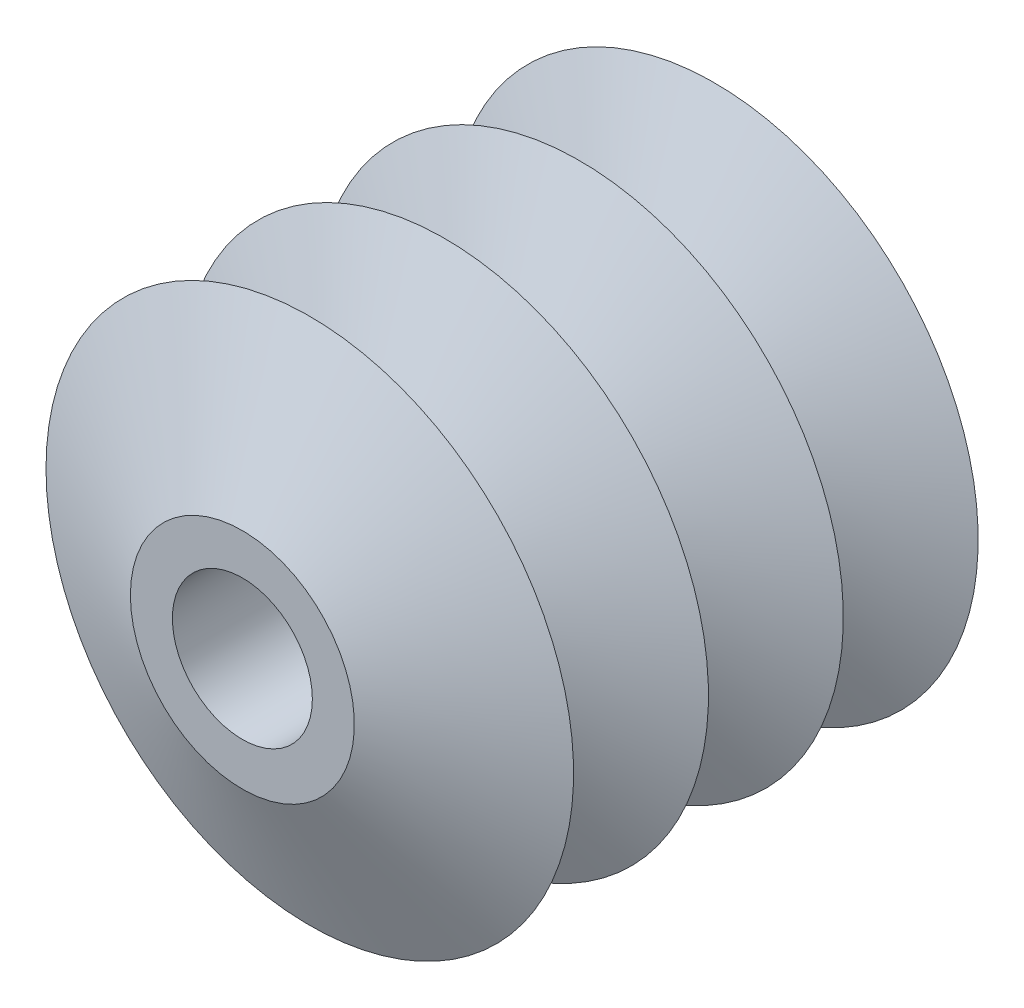
SolidWorks part; units mm, degrees
ref_plane "Front Plane" through (0, 0, 0) normal (0, 0, 1) x (1, 0, 0)
ref_plane "Top Plane" through (0, 0, 0) normal (0, 1, 0) x (1, 0, 0)
ref_plane "Right Plane" through (0, 0, 0) normal (1, 0, 0) x (0, 0, -1)
sketch "Croquis1" plane through (0, 0, 0) normal (0, 1, 0) x (1, 0, 0)
  line L0 (0, 33.7213) -> (0, -33.7213)
  line L1 (0, 33.7213) -> (14, 33.7213)
  line L2 (0, -33.7213) -> (14, -33.7213)
  line L9 (14, -33.7213) -> (32.9802, -25.291)
  line L10 (32.9802, -25.291) -> (14, -16.8606)
  line L11 (14, -16.8606) -> (32.9802, -8.4303)
  line L12 (32.9802, -8.4303) -> (14, 0)
  line L13 (14, 0) -> (32.9802, 8.4303)
  line L14 (32.9802, 8.4303) -> (14, 16.8606)
  line L15 (14, 16.8606) -> (32.9802, 25.291)
  line L16 (32.9802, 25.291) -> (14, 33.7213)
  point P4 (0, 0)
  point P14 (0, 0)
  point P15 (0, 0)
  point P16 (0, 0)
  point P17 (0, 0)
  dimension "D1" = 14
revolve "Revolución3" add sketch "Croquis1" angle 360 about L0
hole_wizard "Taladro de margen para M162" positions "Croquis8" profile "Croquis7" hole size "M16" standard "ISO" end condition through all
sketch "Croquis8" plane through (0, 0, 33.7213) normal (0, 0, 1) x (1, 0, 0)
  point P0 (0, 0.1296)
sketch "Croquis7" plane through (0, 0.1296, 33.7213) normal (1, 0, 0) x (0, -1, 0)
  line L0 (0, 0) -> (0, 67.4426)
  line L1 (0, 67.4426) -> (8.75, 67.4426)
  line L2 (8.75, 67.4426) -> (8.75, 0)
  line L5 (8.75, 0) -> (0, 0)
  line L11 (0, -6.35) -> (0, 107.95) construction
  dimension "Diámetro de taladro hasta el siguiente" = 17.5
  dimension "Profundidad de taladro hasta el siguiente" = 67.4426
